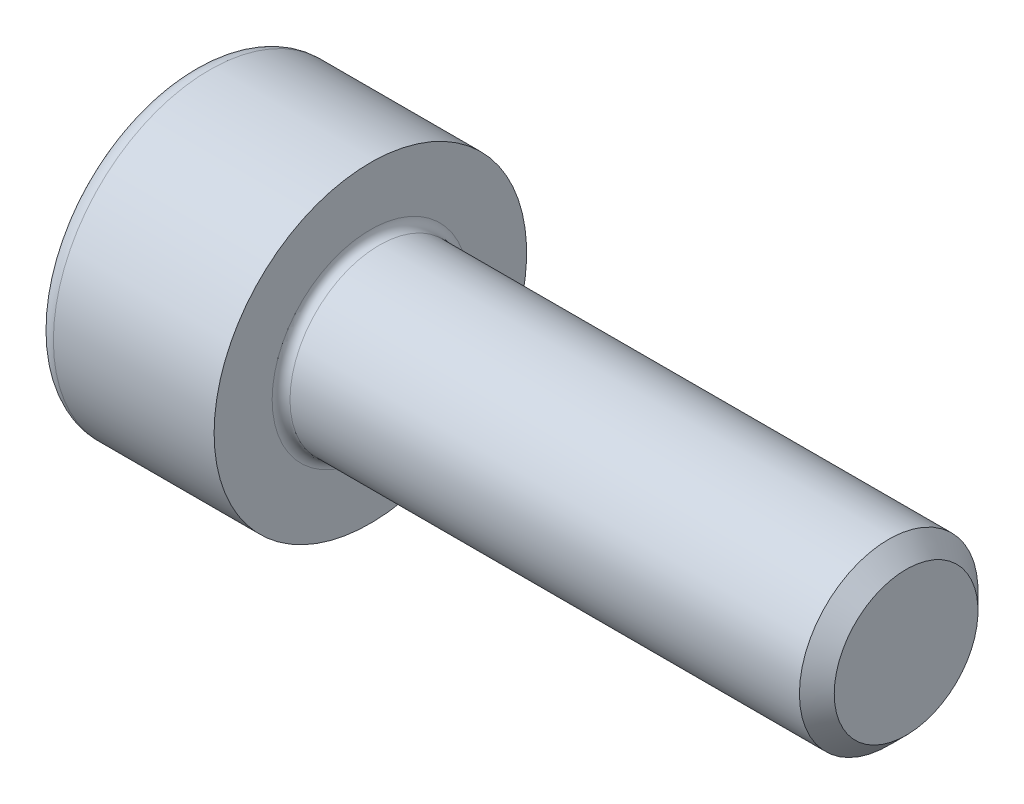
SolidWorks part; units mm, degrees
revolve "Base-Revolve" add sketch "BodySke"
sketch "BodySke" plane through (0, 0, 0) normal (0, 0, 1) x (1, 0, 0)
  line L0 (0, 0) -> (0, 3.5)
  line L1 (0, 3.5) -> (4, 3.5)
  line L2 (4, 3.5) -> (4, 2)
  line L3 (4, 2) -> (15.61, 2)
  line L4 (16, 1.61) -> (16, 0)
  line L5 (16, 0) -> (0, 0)
  line L6 (-31.75, 0) -> (127, 0) construction
  line L8 (16, 1.61) -> (15.61, 2)
  line L10 (16, -1.61) -> (15.61, -2) construction
  line L11 (4.7, 9.525) -> (4.7, 3.175) construction
  line L12 (4, 9.525) -> (4, 3.175) construction
  line L13 (-44, 9.525) -> (-44, 3.175) construction
  dimension "Head_ht" = 4
  dimension "Length" = 12
  dimension "Body_ch_ang" = 45
  dimension "Diameter" = 4
  dimension "Minor_dia" = 3.22
  dimension "Advance" = 0.7
  dimension "Thread_nom" = 12
  dimension "Thread_length" = 60
  dimension "Head_dia" = 7
cosmetic thread "ThreadCosmetic"
fillet "Fillet1" radius 0.2 1 edges at (4, 0, 2)
fillet "Fillet2" radius 0.4 1 edges at (0, 0, 3.5)
ref_plane "Plane1" through (0, 0, 0) normal (0, 0, 1) x (1, 0, 0)
ref_plane "Plane2" through (0, 0, 0) normal (0, 1, 0) x (1, 0, 0)
ref_plane "Plane3" through (0, 0, 0) normal (1, 0, 0) x (0, 0, -1)
sketch "Sketch2" plane through (0, 0, 0) normal (0, 0, 1) x (1, 0, 0)
  line L0 (0, 1.51) -> (2, 1.51)
  line L1 (2, 1.51) -> (2.8718, 0)
  line L2 (-31.75, 0) -> (127, 0) construction
  line L3 (2.8718, 0) -> (0, 0)
  line L4 (0, 0) -> (0, 1.51)
  line L6 (0, 0) -> (47.625, 0) construction
  dimension "D1" = 1.51
  dimension "D2" = 60
  dimension "Depth" = 2
revolve "Hex-PreBroach" cut sketch "Sketch2" angle 360 about L6
sketch "Sketch3" plane through (0, 0, 0) normal (-1, 0, 0) x (0, 0.5, 0.866)
  line L0 (0.8718, 1.51) -> (-0.8718, 1.51)
  line L1 (-0.8718, 1.51) -> (-1.7436, 0)
  line L2 (0.8718, 1.51) -> (1.7436, 0)
  line L3 (0.8718, -1.51) -> (1.7436, 0)
  line L4 (0.8718, -1.51) -> (-0.8718, -1.51)
  line L5 (-0.8718, -1.51) -> (-1.7436, 0)
  dimension "D1" = 1.51
  dimension "D2" = 1.51
  dimension "Hex_size" = 3.02
extrude "Hex" cut sketch "Sketch3" against normal blind 2
sketch "ThdSchSke" plane through (0, 0, 0) normal (0, 0, 1) x (1, 0, 0)
  line L0 (6.1, -1.61) -> (5.8269, -2)
  line L1 (6.1, -1.61) -> (6.3731, -2)
  line L2 (6.3731, -2) -> (6.3731, -2.5)
  line L3 (-3.175, 0) -> (5.1513, 0) construction
  line L4 (0, 3.1) -> (0, -3.1) construction
  line L5 (6.3731, -2.5) -> (5.8269, -2.5)
  line L6 (5.8269, -2.5) -> (5.8269, -2)
  dimension "Thread_minor" = 3.22
  dimension "Diameter" = 4
  dimension "Start" = 6.1
revolve "ThreadSchematic" [suppressed] cut sketch "ThdSchSke" angle 360 about L3
pattern_linear "ThdSchPat" [suppressed]
equation "\"D2@Sketch3\" = \"Hex_size@Sketch3\" / 2"
equation "\"D1@Sketch3\" = \"Hex_size@Sketch3\" / 2"
equation "\"D1@Sketch2\" = \"Hex_size@Sketch3\" / 2"
equation "\"Thread_minor@ThreadCosmetic\"  =  \"Minor_dia@BodySke\""
equation "\"Depth@Sketch2\" =  \"Key_eng@Hex\""
equation "\"Thread_length@ThreadCosmetic\" = ((sgn( (\"Length@BodySke\" - \"Advance@BodySke\" * 3.0) - \"Thread_nom@BodySke\" )-1)*( (\"Length@BodySke\" - \"Advance@BodySke\" * 3.0) - \"Thread_nom@BodySke\" ))/-2+ \"Thread_nom@BodySke\""
equation "\"Thread_minor@ThdSchSke\" = \"Minor_dia@BodySke\""
equation "\"Diameter@ThdSchSke\" = \"Diameter@BodySke\""
equation "\"Overcut@ThdSchSke\" = \"Diameter@BodySke\" * 1.25"
equation "\"Start@ThdSchSke\" = \"Head_ht@BodySke\" + \"Length@BodySke\" - \"Thread_length@ThreadCosmetic\"  '---Non-countersunk---"
equation "\"Num_threads@ThdSchPat\" = int( \"Thread_length@ThreadCosmetic\" / \"Advance@BodySke\" + 0.999 )  + 1"
equation "\"Advance@ThdSchPat\" = \"Thread_length@ThreadCosmetic\" /  (\"Num_threads@ThdSchPat\" - 1) 'relax it"
equation "\"Num_threads@ThdSchPat\" = \"Num_threads@ThdSchPat\" - sgn( \"Num_threads@ThdSchPat\" - 1) '---chamfered tips only---"
